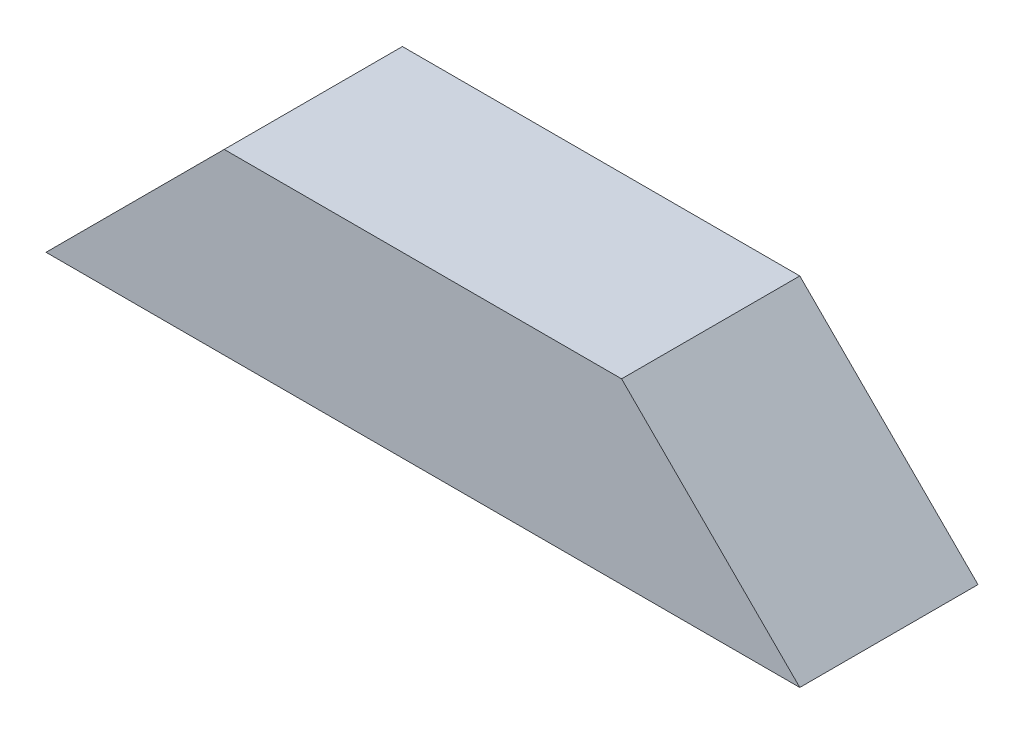
SolidWorks part; units mm, degrees
ref_plane "前视基准面" through (0, 0, 0) normal (0, 0, 1) x (1, 0, 0)
ref_plane "上视基准面" through (0, 0, 0) normal (0, 1, 0) x (1, 0, 0)
ref_plane "右视基准面" through (0, 0, 0) normal (1, 0, 0) x (0, 0, -1)
sketch "草图1" plane through (0, 0, 0) normal (0, 0, 1) x (1, 0, 0)
  line L0 (38.3435, 49.9221) -> (80.6435, 49.9221)
  line L1 (48.3435, 59.9221) -> (70.6435, 59.9221)
  line L2 (38.3435, 49.9221) -> (48.3435, 59.9221)
  line L3 (80.6435, 49.9221) -> (70.6435, 59.9221)
  dimension "D1" = 10
  dimension "D2" = 42.3
extrude "凸台-拉伸1" add sketch "草图1" along normal blind 10
